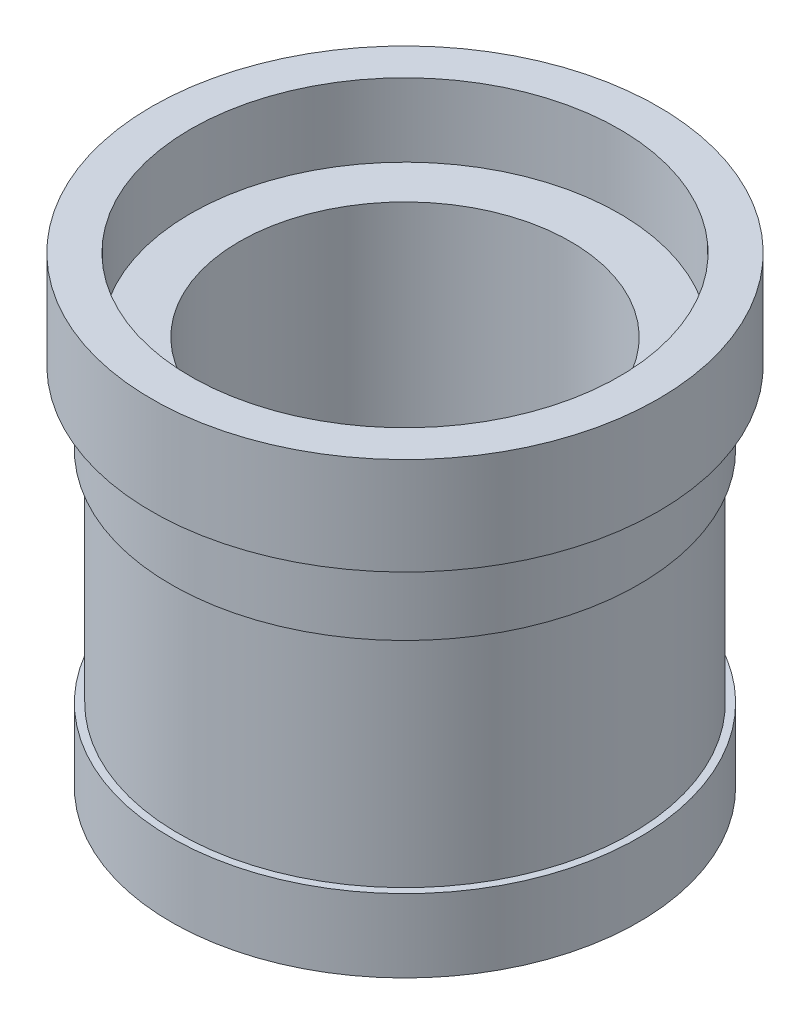
SolidWorks part; units mm, degrees
ref_plane "Front Plane" through (0, 0, 0) normal (0, 0, 1) x (1, 0, 0)
ref_plane "Top Plane" through (0, 0, 0) normal (0, 1, 0) x (1, 0, 0)
ref_plane "Right Plane" through (0, 0, 0) normal (1, 0, 0) x (0, 0, -1)
sketch "Sketch1" plane through (0, 0, 0) normal (0, 0, 1) x (1, 0, 0)
  line L0 (0, 74.8007) -> (0, -29.7164) construction
  line L1 (34, 0) -> (48, 0)
  line L2 (48, 0) -> (48, 15)
  line L3 (48, 15) -> (46.5, 15)
  line L4 (46.5, 15) -> (46.5, 60)
  line L5 (46.5, 60) -> (48, 60)
  line L6 (48, 60) -> (48, 75)
  line L7 (48, 75) -> (52, 75)
  line L8 (52, 75) -> (52, 95)
  line L9 (52, 95) -> (44, 95)
  line L10 (44, 95) -> (44, 80)
  line L11 (44, 80) -> (34, 80)
  line L12 (34, 80) -> (34, 0)
  point P13 (0, 0)
  point P16 (0, 0)
  point P17 (0, 0)
  point P18 (0, 0)
  point P21 (44.2297, 15.8653)
  dimension "D1" = 34
  dimension "D2" = 14
  dimension "D3" = 15
  dimension "D4" = 1.5
  dimension "D5" = 45
  dimension "D6" = 1.5
  dimension "D7" = 15
  dimension "D8" = 4
  dimension "D9" = 20
  dimension "D10" = 8
  dimension "D11" = 15
revolve "Revolve1" add sketch "Sketch1" angle 360 about L0
